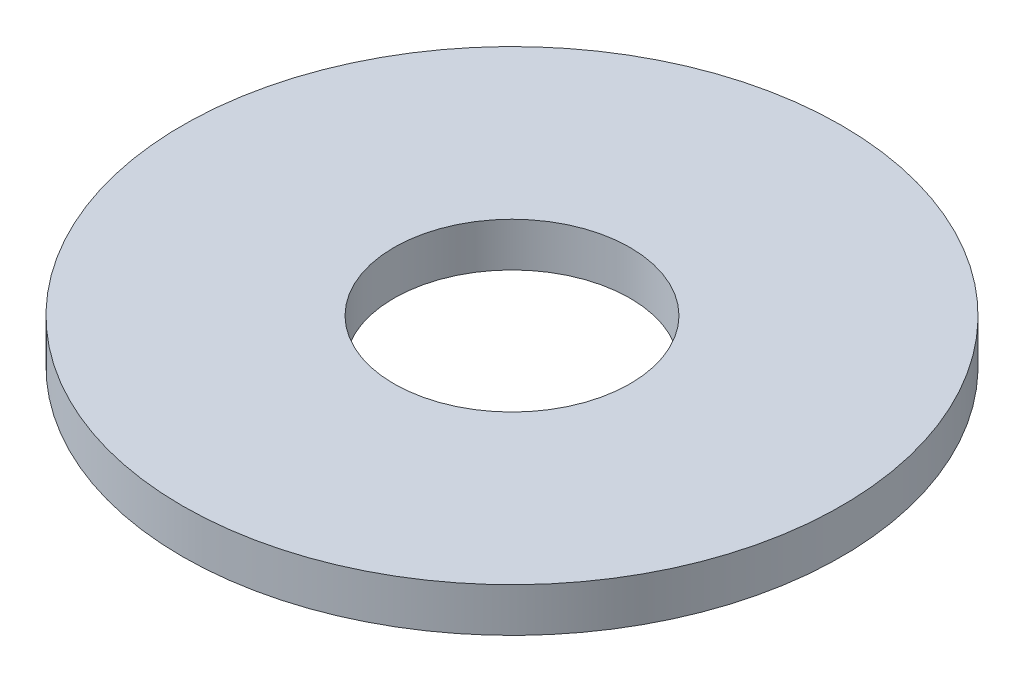
SolidWorks part; units mm, degrees
ref_plane "Piano frontale" through (0, 0, 0) normal (0, 0, 1) x (1, 0, 0)
ref_plane "Piano superiore" through (0, 0, 0) normal (0, 1, 0) x (1, 0, 0)
ref_plane "Piano destro" through (0, 0, 0) normal (1, 0, 0) x (0, 0, -1)
sketch "Schizzo1" plane through (0, 0, 0) normal (0, 1, 0) x (1, 0, 0)
  circle A0 centre (0, 0) radius 2.15
  circle A1 centre (0, 0) radius 6
extrude "Estrusione-Estrusione1" add sketch "Schizzo1" along normal blind 0.8
scale "Scale3" scale about centroid uniform scaling yes scale factor 1.5
